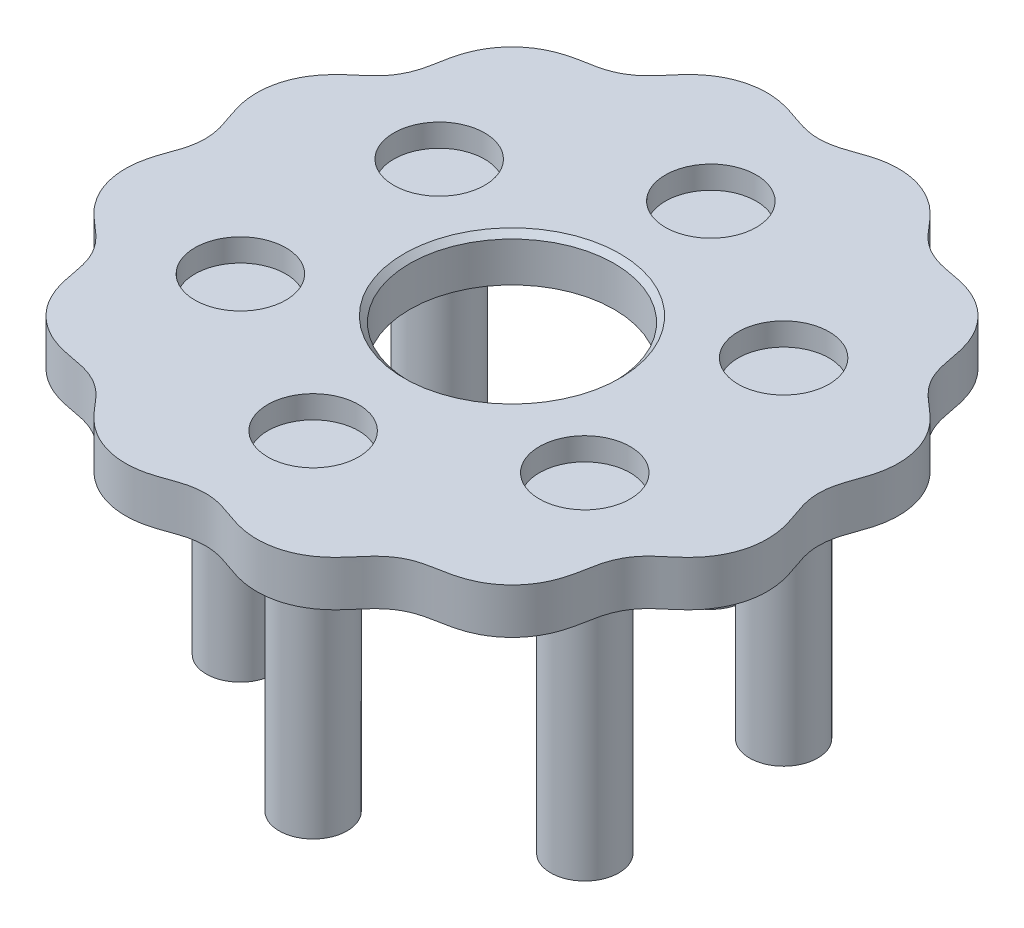
SolidWorks part; units mm, degrees
ref_plane "Front Plane" through (0, 0, 0) normal (0, 0, 1) x (1, 0, 0)
ref_plane "Top Plane" through (0, 0, 0) normal (0, 1, 0) x (1, 0, 0)
ref_plane "Right Plane" through (0, 0, 0) normal (1, 0, 0) x (0, 0, -1)
sketch "Sketch1" plane through (0, 0, 0) normal (0, 1, 0) x (1, 0, 0)
  spline S0 degree 4 poles (22.6635, 15.5278) (22.694, 15.3764) (22.7597, 15.075) (22.9168, 14.4769) (23.2668, 13.6156) (23.8682, 12.704) (24.7627, 11.8447) (25.7313, 11.0803) (26.6185, 10.2145) (27.2551, 9.3344) (27.6787, 8.5074) (28.0266, 7.5556) (28.2156, 6.6706) (28.2671, 5.8227) (28.2081, 5.0347) (28.1283, 4.5049) (28.028, 4.036) (27.8872, 3.5336) (27.729, 3.0663) (27.5853, 2.6688) (27.4665, 2.3371) (27.3747, 2.0707) (27.2886, 1.8022) (27.2106, 1.5315) (27.1426, 1.2576) (27.0863, 0.982) (27.0484, 0.7371) (27.0246, 0.528) (27.0108, 0.3549) (27.0034, 0.2052) (26.9997, 0.0497) (26.9997, -0.038) (27.002, -0.1485) (27.0063, -0.2636) (27.0124, -0.3754) (27.0222, -0.4974) (27.0371, -0.6374) (27.0556, -0.7787) (27.0775, -0.9192) (27.1092, -1.0939) (27.1535, -1.3024) (27.2139, -1.5437) (27.293, -1.8166) (27.3802, -2.0871) (27.473, -2.3556) (27.593, -2.6899) (27.7377, -3.0908) (27.8962, -3.5622) (28.0634, -4.1672) (28.1925, -4.8421) (28.2747, -5.787) (28.1885, -6.9907) (27.811, -8.3475) (27.0846, -9.6473) (26.1861, -10.6718) (25.2382, -11.4719) (24.3726, -12.191) (23.6209, -13.0381) (23.063, -14.0252) (22.7232, -15.105) (22.5406, -16.2149) (22.3114, -17.4345) (21.8559, -18.719) (21.0787, -19.9817) (19.9443, -21.1081) (18.6762, -21.8764) (17.3888, -22.3233) (16.1685, -22.5473) (15.0588, -22.7333) (13.9816, -23.082) (12.9996, -23.6488) (12.1589, -24.4072) (11.4429, -25.2751) (10.6388, -26.22) (9.6083, -27.1117) (8.309, -27.8259) (6.7663, -28.2454) (5.2842, -28.2873) (3.944, -28.0398) (2.7732, -27.6285) (1.7207, -27.2316) (0.6156, -26.9859) (-0.5181, -26.9752) (-1.6276, -27.2025) (-2.6832, -27.5925) (-3.8501, -28.0135) (-5.1865, -28.2795) (-6.6753, -28.2589) (-8.2357, -27.8569) (-9.5567, -27.1493) (-10.6077, -26.2531) (-11.4243, -25.2991) (-12.1455, -24.4207) (-12.9931, -23.6523) (-13.9851, -23.0793) (-15.0742, -22.7291) (-16.1955, -22.5435) (-17.43, -22.3137) (-18.7318, -21.8518) (-20.0054, -21.0621) (-21.1341, -19.9121) (-21.8967, -18.6332) (-22.3348, -17.343) (-22.5539, -16.122) (-22.7438, -15.0128) (-23.1013, -13.9382) (-23.677, -12.9614) (-24.4421, -12.127) (-25.312, -11.4138) (-26.2537, -10.6057) (-27.1385, -9.5692) (-27.8436, -8.2648) (-28.2522, -6.7192) (-28.2837, -5.2368) (-28.0272, -3.8985) (-27.6111, -2.7296) (-27.2174, -1.6756) (-26.9805, -0.5684) (-26.9801, 0.5654) (-27.2164, 1.6727) (-27.61, 2.7268) (-28.0264, 3.8955) (-28.2835, 5.2338) (-28.2526, 6.7162) (-27.8447, 8.262) (-27.1402, 9.5666) (-26.2559, 10.6035) (-25.3144, 11.412) (-24.4444, 12.125) (-23.6789, 12.959) (-23.1026, 13.9354) (-22.7445, 15.0098) (-22.5543, 16.119) (-22.3356, 17.34) (-21.898, 18.6305) (-21.1359, 19.9097) (-20.0078, 21.0601) (-18.7346, 21.8505) (-17.433, 22.3129) (-16.1985, 22.5431) (-15.0772, 22.7284) (-13.9879, 23.0781) (-12.9955, 23.6505) (-12.1476, 24.4184) (-11.4261, 25.2967) (-10.6099, 26.251) (-9.5592, 27.1476) (-8.2386, 27.8558) (-6.6784, 28.2585) (-5.1895, 28.2798) (-3.853, 28.0143) (-2.686, 27.5936) (-1.6305, 27.2034) (-0.5212, 26.9755) (0.6126, 26.9855) (1.7178, 27.2307) (2.7704, 27.6274) (3.9411, 28.039) (5.2811, 28.2871) (6.7633, 28.2458) (8.3061, 27.8271) (9.6058, 27.1134) (10.6367, 26.2222) (11.441, 25.2775) (12.1568, 24.4095) (12.9971, 23.6506) (13.9788, 23.0832) (15.0559, 22.734) (16.1654, 22.5477) (17.3858, 22.324) (18.6734, 21.8778) (19.9419, 21.11) (21.0768, 19.9841) (21.8546, 18.7217) (22.3106, 17.4375) (22.5401, 16.2179) (22.7225, 15.1079) (23.0618, 14.028) (23.6191, 13.0406) (24.3704, 12.1931) (25.2358, 11.4738) (26.1839, 10.6739) (27.0829, 9.6498) (27.8098, 8.3504) (28.1879, 6.9938) (28.2746, 5.7903) (28.193, 4.8455) (28.0642, 4.1706) (27.8972, 3.5657) (27.7163, 3.0268) (27.521, 2.4935) (27.3561, 2.024) (27.2322, 1.6167) (27.1458, 1.2711) (27.0884, 0.9947) (27.0442, 0.7102) (27.0198, 0.4861) (27.0079, 0.3062) (27.0022, 0.1528) (26.9997, 0.042) (26.9996, -0.0456) (27.0032, -0.201) (27.0105, -0.3509) (27.0242, -0.5239) (27.0479, -0.733) (27.0856, -0.978) (27.1417, -1.2536) (27.2095, -1.5276) (27.2874, -1.7983) (27.3734, -2.0668) (27.4652, -2.3333) (27.5839, -2.665) (27.7277, -3.0625) (27.8859, -3.5297) (28.0537, -4.1271) (28.1849, -4.7916) (28.2731, -5.7196) (28.2068, -6.8215) (27.9166, -8.0047) (27.3482, -9.2051) (26.6211, -10.2114) (25.7344, -11.0777) (24.7659, -11.8422) (23.8708, -12.7009) (23.2688, -13.612) (22.9181, -14.473) (22.7607, -15.0711) (22.6948, -15.3725) (22.6643, -15.5239) knots 0 0 0 0 0 0.002811 0.005621 0.011242 0.016863 0.022484 0.028105 0.033725 0.039346 0.042156 0.044966 0.052152 0.055745 0.057541 0.059337 0.061903 0.064469 0.067035 0.068318 0.069601 0.070884 0.072167 0.07345 0.074733 0.076016 0.077299 0.07794 0.078582 0.079223 0.079864 0.080511 0.080835 0.081158 0.081805 0.082451 0.083098 0.083745 0.084391 0.085038 0.086332 0.087625 0.088918 0.090212 0.091505 0.092799 0.095386 0.097972 0.100559 0.10422 0.107881 0.115202 0.122411 0.12962 0.134741 0.139863 0.144984 0.150105 0.155226 0.160347 0.165468 0.170589 0.177799 0.185008 0.192217 0.199426 0.204547 0.209668 0.214789 0.21991 0.225032 0.230153 0.235274 0.240395 0.247604 0.254813 0.262022 0.269231 0.274352 0.279474 0.284595 0.289716 0.294837 0.299958 0.305079 0.310201 0.31741 0.324619 0.33194 0.339262 0.344435 0.349609 0.354783 0.359956 0.36513 0.370304 0.375477 0.380651 0.387973 0.395294 0.402503 0.409712 0.414833 0.419955 0.425076 0.430197 0.435318 0.440439 0.44556 0.450681 0.45789 0.465099 0.472309 0.479518 0.484639 0.48976 0.494881 0.500002 0.505123 0.510245 0.515366 0.520487 0.527696 0.534905 0.542114 0.549323 0.554444 0.559565 0.564686 0.569808 0.574929 0.58005 0.585171 0.590293 0.597502 0.604711 0.612032 0.619353 0.624527 0.629701 0.634875 0.640048 0.645222 0.650396 0.655569 0.660743 0.668064 0.675386 0.682595 0.689804 0.694925 0.700046 0.705168 0.710289 0.71541 0.720531 0.725652 0.730773 0.737982 0.745191 0.752401 0.75961 0.764731 0.769852 0.774973 0.780094 0.785215 0.790337 0.795458 0.800579 0.807788 0.814997 0.822206 0.829415 0.834536 0.839657 0.844778 0.849899 0.855021 0.860142 0.865263 0.870384 0.877594 0.884803 0.892123 0.895783 0.899443 0.90203 0.904616 0.907203 0.909789 0.912376 0.913669 0.914962 0.916256 0.917549 0.918842 0.919165 0.919489 0.920135 0.920777 0.921418 0.92206 0.922701 0.923984 0.925267 0.92655 0.927833 0.929116 0.930399 0.931682 0.932965 0.935531 0.938097 0.940662 0.944255 0.947848 0.955033 0.960654 0.966274 0.971895 0.977516 0.983137 0.988758 0.994379 0.997189 1 1 1 1 1 construction
  spline S1 degree 4 poles (27, 0) (27, -0.0298) (27.0005, -0.0746) (27.002, -0.1485) (27.0063, -0.2636) (27.0124, -0.3754) (27.0222, -0.4974) (27.0371, -0.6374) (27.0556, -0.7787) (27.0775, -0.9192) (27.1092, -1.0939) (27.1535, -1.3024) (27.2139, -1.5437) (27.293, -1.8166) (27.3802, -2.0871) (27.473, -2.3556) (27.593, -2.6899) (27.7377, -3.0908) (27.8962, -3.5622) (28.0634, -4.1672) (28.1925, -4.8421) (28.2747, -5.787) (28.1885, -6.9907) (27.811, -8.3475) (27.0846, -9.6473) (26.1861, -10.6718) (25.2382, -11.4719) (24.3726, -12.191) (23.6209, -13.0381) (23.063, -14.0252) (22.7232, -15.105) (22.5406, -16.2149) (22.3114, -17.4345) (21.8559, -18.719) (21.0787, -19.9817) (19.9443, -21.1081) (18.6762, -21.8764) (17.3888, -22.3233) (16.1685, -22.5473) (15.0588, -22.7333) (13.9816, -23.082) (12.9996, -23.6488) (12.1589, -24.4072) (11.4429, -25.2751) (10.6388, -26.22) (9.6083, -27.1117) (8.309, -27.8259) (6.7663, -28.2454) (5.2842, -28.2873) (3.944, -28.0398) (2.7732, -27.6285) (1.7207, -27.2316) (0.6156, -26.9859) (-0.5181, -26.9752) (-1.6276, -27.2025) (-2.6832, -27.5925) (-3.8501, -28.0135) (-5.1865, -28.2795) (-6.6753, -28.2589) (-8.2357, -27.8569) (-9.5567, -27.1493) (-10.6077, -26.2531) (-11.4243, -25.2991) (-12.1455, -24.4207) (-12.9931, -23.6523) (-13.9851, -23.0793) (-15.0742, -22.7291) (-16.1955, -22.5435) (-17.43, -22.3137) (-18.7318, -21.8518) (-20.0054, -21.0621) (-21.1341, -19.9121) (-21.8967, -18.6332) (-22.3348, -17.343) (-22.5539, -16.122) (-22.7438, -15.0128) (-23.1013, -13.9382) (-23.677, -12.9614) (-24.4421, -12.127) (-25.312, -11.4138) (-26.2537, -10.6057) (-27.1385, -9.5692) (-27.8436, -8.2648) (-28.2522, -6.7192) (-28.2837, -5.2368) (-28.0272, -3.8985) (-27.6111, -2.7296) (-27.2174, -1.6756) (-26.9805, -0.5684) (-26.9801, 0.5654) (-27.2164, 1.6727) (-27.61, 2.7268) (-28.0264, 3.8955) (-28.2835, 5.2338) (-28.2526, 6.7162) (-27.8447, 8.262) (-27.1402, 9.5666) (-26.2559, 10.6035) (-25.3144, 11.412) (-24.4444, 12.125) (-23.6789, 12.959) (-23.1026, 13.9354) (-22.7445, 15.0098) (-22.5543, 16.119) (-22.3356, 17.34) (-21.898, 18.6305) (-21.1359, 19.9097) (-20.0078, 21.0601) (-18.7346, 21.8505) (-17.433, 22.3129) (-16.1985, 22.5431) (-15.0772, 22.7284) (-13.9879, 23.0781) (-12.9955, 23.6505) (-12.1476, 24.4184) (-11.4261, 25.2967) (-10.6099, 26.251) (-9.5592, 27.1476) (-8.2386, 27.8558) (-6.6784, 28.2585) (-5.1895, 28.2798) (-3.853, 28.0143) (-2.686, 27.5936) (-1.6305, 27.2034) (-0.5212, 26.9755) (0.6126, 26.9855) (1.7178, 27.2307) (2.7704, 27.6274) (3.9411, 28.039) (5.2811, 28.2871) (6.7633, 28.2458) (8.3061, 27.8271) (9.6058, 27.1134) (10.6367, 26.2222) (11.441, 25.2775) (12.1568, 24.4095) (12.9971, 23.6506) (13.9788, 23.0832) (15.0559, 22.734) (16.1654, 22.5477) (17.3858, 22.324) (18.6734, 21.8778) (19.9419, 21.11) (21.0768, 19.9841) (21.8546, 18.7217) (22.3106, 17.4375) (22.5401, 16.2179) (22.7225, 15.1079) (23.0618, 14.028) (23.6191, 13.0406) (24.3704, 12.1931) (25.2358, 11.4738) (26.1839, 10.6739) (27.0829, 9.6498) (27.8098, 8.3504) (28.1879, 6.9938) (28.2746, 5.7903) (28.193, 4.8455) (28.0642, 4.1706) (27.8972, 3.5657) (27.7163, 3.0268) (27.521, 2.4935) (27.3561, 2.024) (27.2322, 1.6167) (27.1458, 1.2711) (27.0884, 0.9947) (27.0442, 0.7102) (27.0198, 0.4861) (27.0079, 0.3062) (27.0022, 0.1528) (27.0005, 0.0787) (27, 0.0339) (27, 0.0041) knots 0.079864 0.079864 0.079864 0.079864 0.079864 0.080511 0.080835 0.081158 0.081805 0.082451 0.083098 0.083745 0.084391 0.085038 0.086332 0.087625 0.088918 0.090212 0.091505 0.092799 0.095386 0.097972 0.100559 0.10422 0.107881 0.115202 0.122411 0.12962 0.134741 0.139863 0.144984 0.150105 0.155226 0.160347 0.165468 0.170589 0.177799 0.185008 0.192217 0.199426 0.204547 0.209668 0.214789 0.21991 0.225032 0.230153 0.235274 0.240395 0.247604 0.254813 0.262022 0.269231 0.274352 0.279474 0.284595 0.289716 0.294837 0.299958 0.305079 0.310201 0.31741 0.324619 0.33194 0.339262 0.344435 0.349609 0.354783 0.359956 0.36513 0.370304 0.375477 0.380651 0.387973 0.395294 0.402503 0.409712 0.414833 0.419955 0.425076 0.430197 0.435318 0.440439 0.44556 0.450681 0.45789 0.465099 0.472309 0.479518 0.484639 0.48976 0.494881 0.500002 0.505123 0.510245 0.515366 0.520487 0.527696 0.534905 0.542114 0.549323 0.554444 0.559565 0.564686 0.569808 0.574929 0.58005 0.585171 0.590293 0.597502 0.604711 0.612032 0.619353 0.624527 0.629701 0.634875 0.640048 0.645222 0.650396 0.655569 0.660743 0.668064 0.675386 0.682595 0.689804 0.694925 0.700046 0.705168 0.710289 0.71541 0.720531 0.725652 0.730773 0.737982 0.745191 0.752401 0.75961 0.764731 0.769852 0.774973 0.780094 0.785215 0.790337 0.795458 0.800579 0.807788 0.814997 0.822206 0.829415 0.834536 0.839657 0.844778 0.849899 0.855021 0.860142 0.865263 0.870384 0.877594 0.884803 0.892123 0.895783 0.899443 0.90203 0.904616 0.907203 0.909789 0.912376 0.913669 0.914962 0.916256 0.917549 0.918842 0.919165 0.919489 0.920135 0.920135 0.920135 0.920135 0.920135
  spline S2 degree 1 poles (27, 0.0041) (27, 0) knots 0 0 1 1
extrude "Boss-Extrude1" add sketch "Sketch1" along normal blind 4
sketch "Sketch2" plane through (0, 4, 0) normal (0, 1, 0) x (1, 0, 0)
  circle A0 centre (0, 0) radius 9
  dimension "D1" = 18
extrude "Cut-Extrude1" cut sketch "Sketch2" against normal blind 4
sketch "Sketch3" plane through (0, 4, 0) normal (0, 1, 0) x (1, 0, 0)
  circle A0 centre (0, 0) radius 17.5 construction
  circle A1 centre (0, 17.5) radius 4
  circle A2 centre (15.1554, 8.75) radius 4
  circle A3 centre (15.1554, -8.75) radius 4
  circle A4 centre (0, -17.5) radius 4
  circle A5 centre (-15.1554, -8.75) radius 4
  circle A6 centre (-15.1554, 8.75) radius 4
  point P17 (0, 0)
  dimension "D1" = 35
  dimension "D2" = 8
  dimension "D3" = 6
extrude "Cut-Extrude2" cut sketch "Sketch3" against normal blind 2
chamfer "Chamfer1" distance 0.5 angle 45 1 edges at (0, 4, 9)
sketch "Sketch4" plane through (0, 0, 0) normal (0, -1, 0) x (1, 0, 0)
  circle A0 centre (0, 17.5) radius 3
  circle A1 centre (15.1554, 8.75) radius 3
  circle A2 centre (15.1554, -8.75) radius 3
  circle A3 centre (0, -17.5) radius 3
  circle A4 centre (-15.1554, -8.75) radius 3
  circle A5 centre (-15.1554, 8.75) radius 3
  point P16 (0, 0)
  dimension "D1" = 6
  dimension "D2" = 6
extrude "Boss-Extrude2" add sketch "Sketch4" along normal blind 25
fillet "Fillet1" radius 1.5 6 edges at (-15.1554, 0, -11.75) (0, 0, -20.5) (15.1554, 0, -11.75) (15.1554, 0, 5.75) (0, 0, 14.5) (-15.1554, 0, 5.75)
